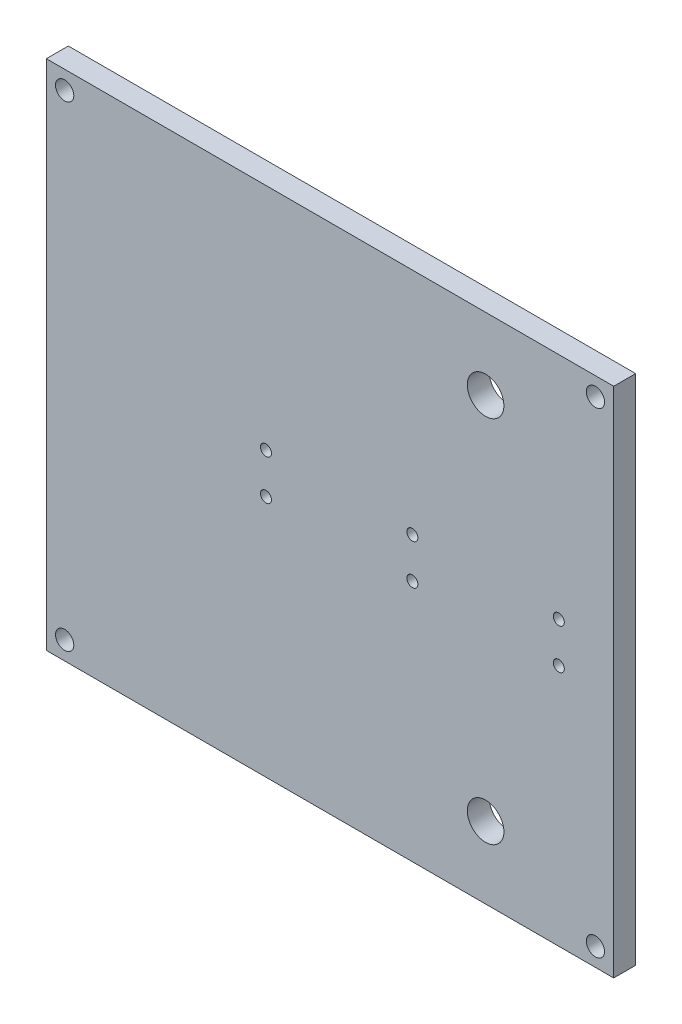
SolidWorks part; units mm, degrees
ref_plane "Plan de face" through (0, 0, 0) normal (0, 0, 1) x (1, 0, 0)
ref_plane "Plan de dessus" through (0, 0, 0) normal (0, 1, 0) x (1, 0, 0)
ref_plane "Plan de droite" through (0, 0, 0) normal (1, 0, 0) x (0, 0, -1)
sketch "Esquisse1" plane through (0, 0, 0) normal (0, 0, 1) x (1, 0, 0)
  line L1 (-77.5, 75.5) -> (77.5, 75.5)
  line L2 (-77.5, 75.5) -> (-77.5, -64.5)
  line L3 (-77.5, -64.5) -> (77.5, -64.5)
  line L4 (77.5, 75.5) -> (77.5, -64.5)
  line L5 (0, 131.3497) -> (0, -131.3497) construction
  circle A0 centre (42.5, -44.9) radius 5
  circle A1 centre (42.5, 55.875) radius 5
  circle A2 centre (-72.5, -59.5) radius 2.5
  circle A3 centre (-72.5, 70.5) radius 2.5
  circle A4 centre (72.5, -59.5) radius 2.5
  circle A5 centre (72.5, 70.5) radius 2.5
  dimension "D3" = 10
  dimension "D8" = 5
  dimension "D12" = 10
  dimension "D17" = 5
  dimension "D1" = 140
  dimension "D2" = 155
  dimension "D4" = 120
  dimension "D5" = 19.6
  dimension "D6" = 77.5
  dimension "D7" = 19.625
  dimension "D9" = 5
  dimension "D10" = 5
  dimension "D11" = 120
  dimension "D13" = 5
  dimension "D14" = 5
  dimension "D15" = 5
  dimension "D16" = 5
  dimension "D18" = 5
extrude "Boss.-Extru.1" add sketch "Esquisse1" along normal blind 6
sketch "Esquisse6" plane through (0, 0, 6) normal (0, 0, 1) x (1, 0, 0)
  line L0 (77.5, -64.5) -> (77.5, 75.5) construction
  line L1 (79.9353, 12.875) -> (-27.4347, 12.875) construction
  line L2 (-27.4347, 1.875) -> (97.1192, 1.875) construction
  circle A0 centre (-17.5, 12.875) radius 1.5
  circle A1 centre (22.5, 12.875) radius 1.5
  circle A2 centre (62.5, 12.875) radius 1.5
  circle A3 centre (62.5, 1.875) radius 1.5
  circle A4 centre (22.5, 1.875) radius 1.5
  circle A5 centre (-17.5, 1.875) radius 1.5
  circle A6 centre (42.5, 55.875) radius 5 construction
  circle A7 centre (42.5, -44.9) radius 5 construction
  dimension "D1" = 3
  dimension "D2" = 3
  dimension "D3" = 3
  dimension "D4" = 3
  dimension "D5" = 3
  dimension "D6" = 3
  dimension "D7" = 40
  dimension "D9" = 15
  dimension "D12" = 15
  dimension "D8" = 40
  dimension "D10" = 40
  dimension "D11" = 40
  dimension "D13" = 43
  dimension "D14" = 46.775
extrude "Enlèv. mat.-Extru.1" cut sketch "Esquisse6" against normal blind 6
